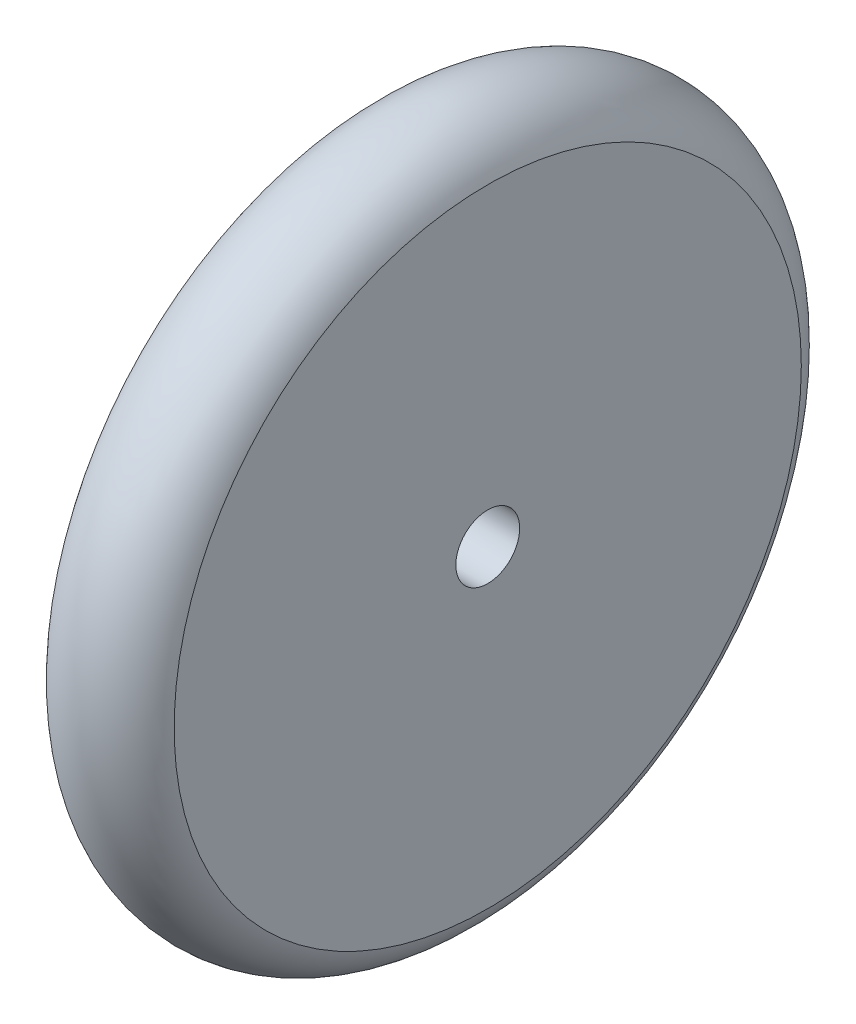
SolidWorks part; units mm, degrees
ref_plane "Plan de face" through (0, 0, 0) normal (0, 0, 1) x (1, 0, 0)
ref_plane "Plan de dessus" through (0, 0, 0) normal (0, 1, 0) x (1, 0, 0)
ref_plane "Plan de droite" through (0, 0, 0) normal (1, 0, 0) x (0, 0, -1)
sketch "Esquisse2" plane through (0, 0, 0) normal (0, 0, 1) x (1, 0, 0)
  line L0 (0, 0) -> (-13.1988, 0) construction
  line L1 (-7.5, 4) -> (-7.5, 39.2906)
  line L2 (7.5, 4) -> (-7.5, 4)
  line L3 (7.5, 4) -> (7.5, 39.2906)
  arc A0 (-7.5, 39.2906) -> (7.5, 39.2906) centre (0, 36.4791) cw
revolve "Révolution1" add sketch "Esquisse2" angle 360 about L0
